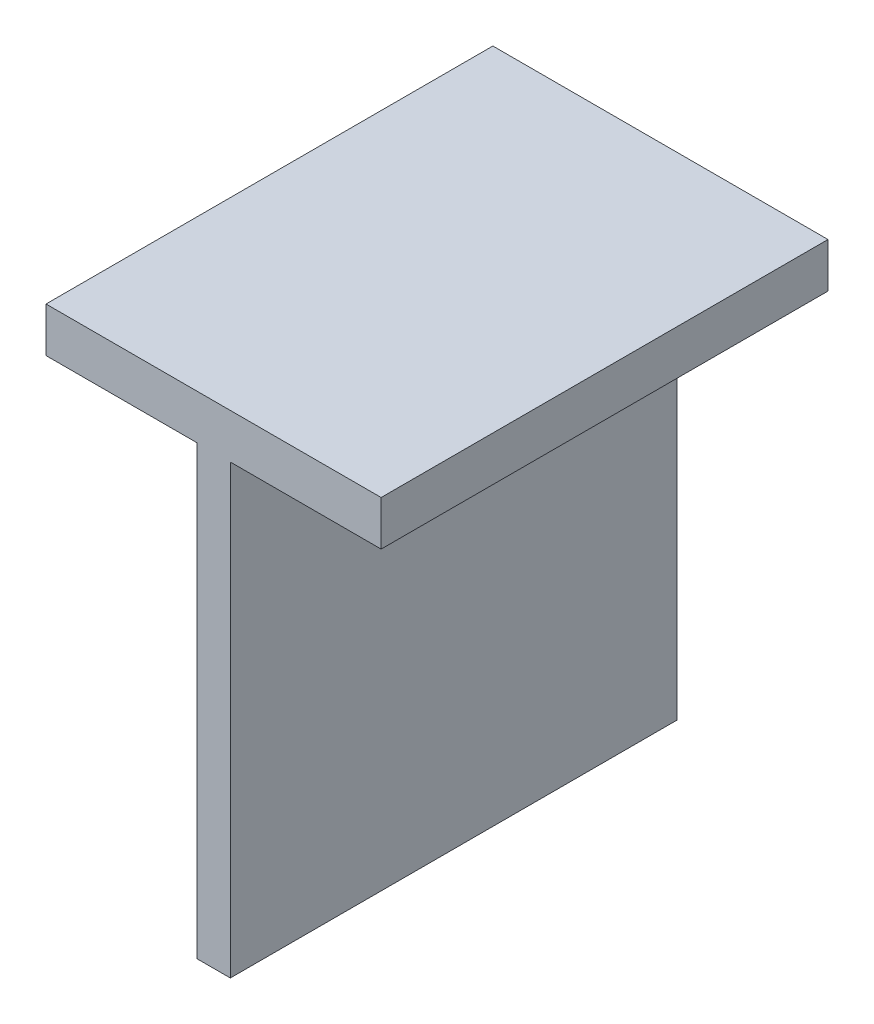
SolidWorks part; units mm, degrees
ref_plane "Front Plane" through (0, 0, 0) normal (0, 0, 1) x (1, 0, 0)
ref_plane "Top Plane" through (0, 0, 0) normal (0, 1, 0) x (1, 0, 0)
ref_plane "Right Plane" through (0, 0, 0) normal (1, 0, 0) x (0, 0, -1)
sketch "Sketch1" plane through (0, 0, 0) normal (0, 0, 1) x (1, 0, 0)
  line L1 (75, 0) -> (75, 2000)
  line L2 (75, 2000) -> (750, 2000)
  line L3 (750, 2000) -> (750, 2200)
  line L4 (750, 2200) -> (-750, 2200)
  line L5 (-750, 2200) -> (-750, 2000)
  line L6 (-750, 2000) -> (-75, 2000)
  line L7 (-75, 2000) -> (-75, 0)
  line L8 (-75, 0) -> (75, 0)
  point P2 (0, 2200)
  point P11 (8.9971, -59.6437)
  point P12 (7.3873, 0)
  dimension "D1" = 150
  dimension "D2" = 2000
  dimension "D3" = 1500
  dimension "D4" = 200
extrude "Boss-Extrude1" add sketch "Sketch1" along normal blind 2000
